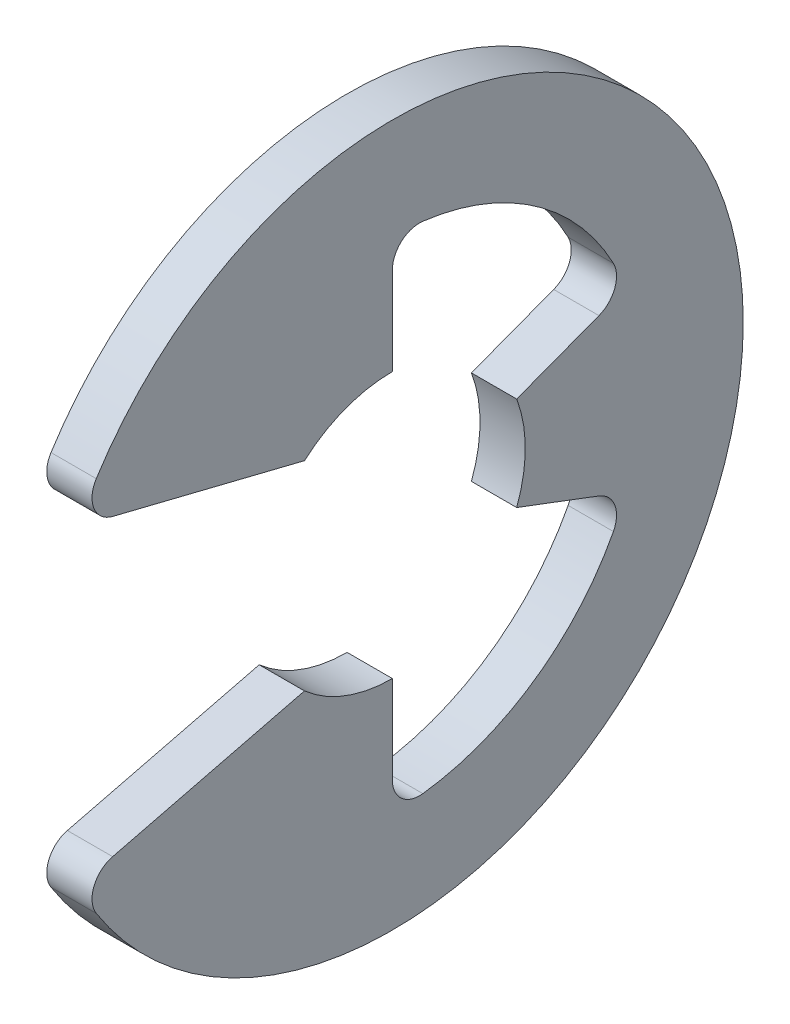
SolidWorks part; units mm, degrees
ref_plane "Front" through (0, 0, 0) normal (0, 0, 1) x (1, 0, 0)
ref_plane "Top" through (0, 0, 0) normal (0, 1, 0) x (1, 0, 0)
ref_plane "Right" through (0, 0, 0) normal (1, 0, 0) x (0, 0, -1)
sketch "Sketch1" plane through (0, 0, 0) normal (1, 0, 0) x (0, 0, -1)
  line L0 (-4.8601, -2.4104) -> (-1.3593, -1.5413)
  line L1 (-4.8601, 2.4104) -> (-1.3593, 1.5413)
  line L2 (0, -2.055) -> (0, -3.8606)
  line L3 (0, 2.055) -> (0, 3.8606)
  line L4 (1.9223, -0.7266) -> (3.6113, -1.3649)
  line L5 (1.9223, 0.7266) -> (3.6113, 1.3649)
  line L6 (0, 0) -> (-5.65, 0) construction
  line L7 (1.9223, 0.7266) -> (1.9223, -0.7266) construction
  line L8 (0, -2.055) -> (-1.3593, -1.5413) construction
  circle A1 centre (0, 0) radius 5.65 construction
  circle A2 centre (0, 0) radius 2.055 construction
  arc A3 (-4.8601, -2.4104) -> (-4.8601, 2.4104) centre (0, 0) ccw
  arc A4 (-1.3593, -1.5413) -> (0, -2.055) centre (0, 0) ccw
  arc A5 (-1.3593, 1.5413) -> (0, 2.055) centre (0, 0) cw
  arc A6 (1.9223, 0.7266) -> (1.9223, -0.7266) centre (0, 0) cw
  arc A7 (0, -3.8606) -> (3.6113, -1.3649) centre (0, 0) ccw
  arc A8 (3.6113, 1.3649) -> (0, 3.8606) centre (0, 0) ccw
  dimension "D" = 4.11
  dimension "D1" = 3.8606
  dimension "OD" = 10.85
  dimension "D2" = 2.3366
  dimension "D3" = 3.0825
extrude "Extrude1" add sketch "Sketch1" along normal mid plane 0.7
fillet "Fillet1" radius 0.42 6 edges at (0, -3.8606, 0) (0, 3.8606, 0) (0, -2.4104, 4.8601) (0, 2.4104, 4.8601) (0, -1.3649, -3.6113) (0, 1.3649, -3.6113)
sketch "Sketch3" plane through (0, 0, 0) normal (0, 1, 0) x (1, 0, 0)
  line L0 (0.37, 3) -> (0.37, 2.5)
  line L1 (0.37, 2.5) -> (-0.37, 2.5)
  line L2 (-0.37, 2.5) -> (-0.37, 3)
  line L3 (-0.37, 3) -> (-5.18, 3)
  line L4 (2.22, 0) -> (2.22, 2.75)
  line L5 (-5.18, 3) -> (-5.18, 0)
  line L6 (-5.18, 0) -> (2.22, 0)
  line L8 (2.22, 0) -> (2.22, 3) construction
  line L9 (2.22, 3) -> (0.37, 3) construction
  line L10 (2.22, 0) -> (17.2631, 0) construction
  line L11 (2.22, 2.75) -> (1.97, 3)
  line L12 (1.97, 3) -> (0.37, 3)
  point P2 (0, 2.5)
  point P5 (0.37, 2.75)
  dimension "D2" = 7.4
  dimension "D1" = 1.85
  dimension "D3" = 45
revolve "Revolve2" [suppressed] add sketch "Sketch3" angle 360 about L10
equation "\"D2@Sketch3\" = \"W@Sketch3\"*10"
equation "\"D1@Sketch3\" = \"D2@Sketch3\"/4"
equation "\"D1@Sketch1\" = (\"OD@Sketch1\"+\"D@Sketch1\")/3.875"
equation "\"D3@Sketch1\" = \"D@Sketch1\"*.75"
equation "\"D1@Fillet1\" = \"D1@Extrude1\"*.6"
